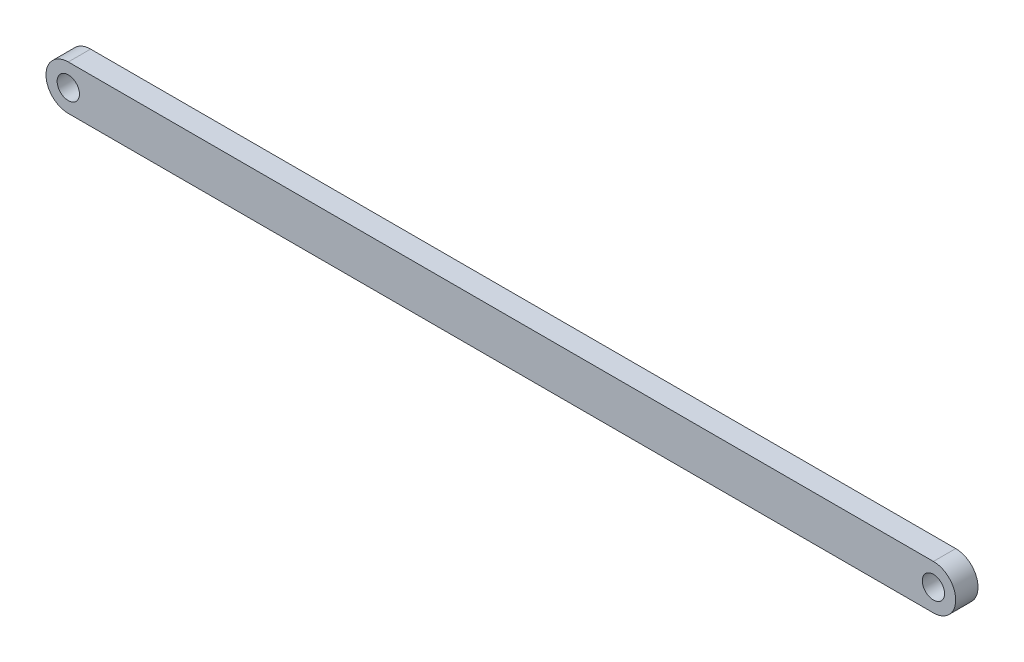
SolidWorks part; units mm, degrees
ref_plane "Plan de face" through (0, 0, 0) normal (0, 0, 1) x (1, 0, 0)
ref_plane "Plan de dessus" through (0, 0, 0) normal (0, 1, 0) x (1, 0, 0)
ref_plane "Plan de droite" through (0, 0, 0) normal (1, 0, 0) x (0, 0, -1)
sketch "Esquisse1" plane through (0, 0, 0) normal (0, 0, 1) x (1, 0, 0)
  line L1 (0, 10) -> (388, 10)
  line L2 (-10, 0.001) -> (-10, 0)
  line L3 (0, -10) -> (388, -10)
  circle A0 centre (0, 0) radius 5
  circle A1 centre (388, 0) radius 5
  arc A2 (0, 10) -> (0, -10) centre (0, 0) ccw
  arc A3 (388, -10) -> (388, 10) centre (388, 0) ccw
  point P11 (-10, -10)
  point P14 (-10, 10)
  dimension "D1" = 10
  dimension "D2" = 10
  dimension "D3" = 388
  dimension "D4" = 20
  dimension "D5" = 10
extrude "Extrusion3" add sketch "Esquisse1" along normal blind 10
